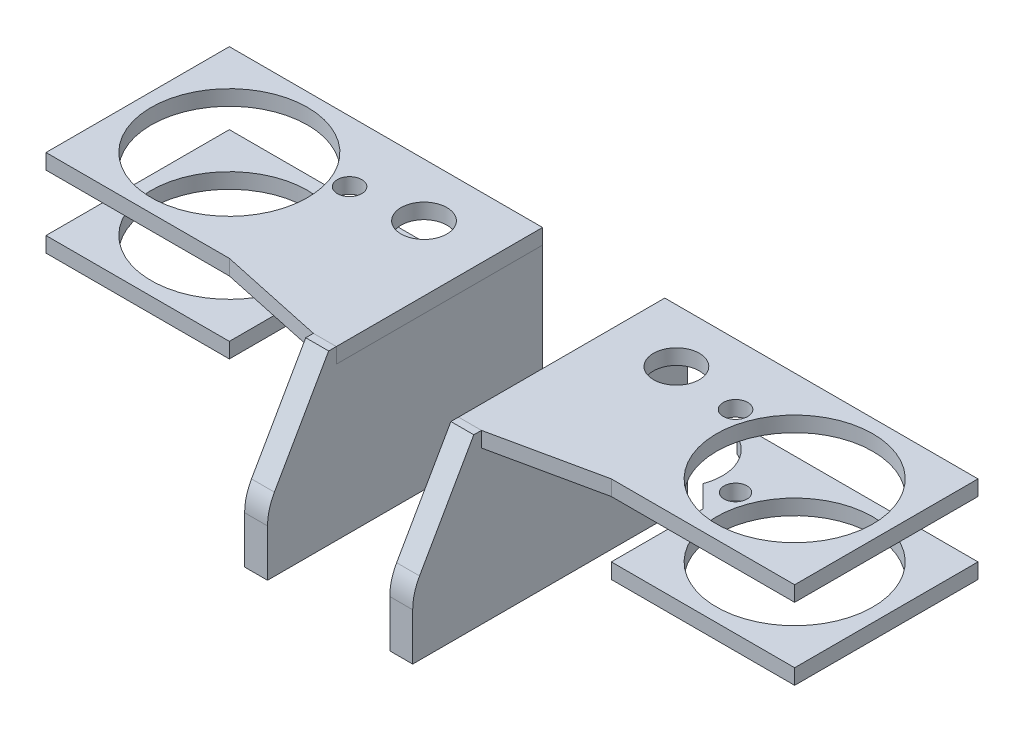
SolidWorks part; units mm, degrees
material "Alum Plate"
ref_plane "Front Plane" through (0, 0, 0) normal (0, 0, 1) x (1, 0, 0)
ref_plane "Top Plane" through (0, 0, 0) normal (0, 1, 0) x (1, 0, 0)
ref_plane "Right Plane" through (0, 0, 0) normal (1, 0, 0) x (0, 0, -1)
sketch "Sketch1" plane through (0, 0, 0) normal (0, 1, 0) x (1, 0, 0)
  line L0 (0, 0) -> (117.475, 0) construction
  line L1 (-117.475, 0) -> (0, 0) construction
  line L3 (-9.525, 158.75) -> (-3.175, 158.75)
  line L4 (-9.525, 158.75) -> (-9.525, 44.45)
  line L5 (-9.525, 44.45) -> (-3.175, 44.45)
  line L6 (-3.175, 158.75) -> (-3.175, 44.45)
  line L7 (-9.525, 158.75) -> (-3.175, 44.45) construction
  line L8 (-9.525, 44.45) -> (-3.175, 158.75) construction
  line L14 (-155.575, -76.2) -> (155.575, -76.2)
  line L18 (-117.475, 0) -> (-52.4506, 15.875) construction
  line L19 (52.4506, 15.875) -> (117.475, 0) construction
  line L20 (-25.4, 38.1) -> (0, 38.1) construction
  line L21 (-6.35, 101.6) -> (0, 101.6)
  line L29 (0, 0) -> (0, -25.4) construction
  line L30 (-117.475, 0) -> (-80.2096, 12.7) construction
  line L43 (-80.2096, 12.7) -> (-52.4506, 15.875) construction
  line L44 (52.4506, 15.875) -> (80.2096, 12.7) construction
  line L55 (80.2096, 12.7) -> (117.475, 0) construction
  line L69 (-155.575, -76.2) -> (-155.575, 38.1)
  line L70 (-155.575, 38.1) -> (155.575, 38.1)
  line L71 (155.575, -76.2) -> (155.575, 38.1)
  line L78 (0, 101.6) -> (0, -25.4)
  line L79 (0, -25.4) -> (0, -152.4) construction
  line L80 (-9.525, -209.55) -> (-3.175, -209.55) construction
  line L81 (-9.525, -209.55) -> (-9.525, -95.25) construction
  line L82 (-9.525, -95.25) -> (-3.175, -95.25) construction
  line L83 (-3.175, -209.55) -> (-3.175, -95.25) construction
  line L84 (-9.525, -209.55) -> (-3.175, -95.25) construction
  line L85 (-9.525, -95.25) -> (-3.175, -209.55) construction
  line L86 (0, -152.4) -> (-6.35, -152.4) construction
  line L87 (-34.925, -76.2) -> (-25.4, -76.2)
  line L88 (-34.925, -76.2) -> (-34.925, 38.1)
  line L89 (-34.925, 38.1) -> (-25.4, 38.1)
  line L90 (-25.4, -76.2) -> (-25.4, 38.1)
  line L91 (34.925, -76.2) -> (25.4, -76.2)
  line L92 (34.925, -76.2) -> (34.925, 38.1)
  line L93 (34.925, 38.1) -> (25.4, 38.1)
  line L94 (25.4, -76.2) -> (25.4, 38.1)
  line L95 (0, 38.1) -> (25.4, 38.1) construction
  circle A0 centre (-117.475, 0) radius 32.5
  circle A1 centre (-117.475, 0) radius 25
  circle A2 centre (117.475, 0) radius 32.5
  circle A3 centre (117.475, 0) radius 25
  circle A4 centre (-52.4506, 15.875) radius 17.5006
  circle A5 centre (52.4506, 15.875) radius 17.5006
  circle A6 centre (-80.2096, 12.7) radius 22.86
  circle A7 centre (80.2096, 12.7) radius 22.86
  point P8 (-6.35, 101.6)
  point P21 (117.475, 32.5)
  point P25 (52.4506, 33.3756)
  point P29 (52.4506, -1.6256)
  point P31 (0, -76.2)
  point P32 (-6.35, -152.4)
  point P62 (149.975, 0)
  dimension "D1" = 50
  dimension "D2" = 65
  dimension "D8" = 35.0012
  dimension "D11" = 127
  dimension "D12" = 63.5
  dimension "D17" = 45.72
  dimension "D3" = 114.3
  dimension "D4" = 6.35
  dimension "D5" = 234.95
  dimension "D6" = 38.1
  dimension "D7" = 38.1
  dimension "D9" = 114.3
  dimension "D10" = 9.525
  dimension "D13" = 9.525
  dimension "D14" = 50.8
  dimension "D15" = 27.94
  dimension "D16" = 39.37
  dimension "D18" = 22.225
  dimension "D19" = 25.4
sketch "Sketch2" plane through (0, 0, 0) normal (1, 0, 0) x (0, 0, -1)
  line L0 (0, 22.225) -> (0, 49.825) construction
  line L1 (-32.5, 53.325) -> (32.5, 53.325)
  line L2 (-32.5, 53.325) -> (-32.5, 46.325)
  line L3 (-32.5, 46.325) -> (32.5, 46.325)
  line L4 (32.5, 53.325) -> (32.5, 46.325)
  line L5 (-32.5, 53.325) -> (32.5, 46.325) construction
  line L6 (-32.5, 46.325) -> (32.5, 53.325) construction
  line L7 (-32.5, 82.55) -> (32.5, 82.55)
  line L8 (-32.5, 82.55) -> (-32.5, 75.55)
  line L9 (-32.5, 75.55) -> (32.5, 75.55)
  line L10 (32.5, 82.55) -> (32.5, 75.55)
  line L11 (-32.5, 82.55) -> (32.5, 75.55) construction
  line L12 (-32.5, 75.55) -> (32.5, 82.55) construction
  line L13 (-25.8191, 0) -> (33.9817, 0) construction
  line L14 (-25.4, 63.5) -> (-152.4, 63.5)
  line L15 (-76.2, 82.55) -> (38.1, 82.55)
  line L16 (-76.2, 82.55) -> (-76.2, 46.325)
  line L17 (-76.2, 46.325) -> (38.1, 46.325)
  line L18 (38.1, 82.55) -> (38.1, 46.325)
  line L19 (-16.2917, 28.7479) -> (-50.301, 31.6992) construction
  line L20 (17.0081, 33.1171) -> (-25.4, 63.5) construction
  line L21 (101.6, 0) -> (-25.4, 0) construction
  line L22 (-76.2, 76.2) -> (38.1, 76.2)
  line L23 (-76.2, 52.675) -> (38.1, 52.675)
  line L24 (-50.301, 31.6992) -> (-25.4, 63.5) construction
  line L25 (-129.1449, 47.625) -> (96, 47.625) construction
  line L32 (-76.2, 12.7) -> (38.1, 12.7)
  line L33 (-76.2, 12.7) -> (-76.2, 9.525)
  line L38 (-76.2, 9.525) -> (38.1, 9.525)
  line L39 (38.1, 12.7) -> (38.1, 9.525)
  line L40 (-1.6256, 31.6992) -> (33.3756, 31.6992)
  line L41 (-1.6256, 31.6992) -> (-1.6256, 76.2)
  line L42 (-1.6256, 76.2) -> (33.3756, 76.2)
  line L43 (33.3756, 31.6992) -> (33.3756, 76.2)
  line L44 (-1.6256, 31.6992) -> (33.3756, 76.2) construction
  line L45 (-1.6256, 76.2) -> (33.3756, 31.6992) construction
  line L46 (-38.1, 82.55) -> (-38.1, 46.325)
  line L47 (-38.1, 64.4375) -> (0, 64.4375) construction
  line L48 (0, 64.4375) -> (38.1, 64.4375) construction
  line L49 (-76.2, 12.7) -> (38.1, 9.525) construction
  line L50 (-76.2, 9.525) -> (38.1, 12.7) construction
  circle A0 centre (0, 22.225) radius 22.225
  circle A2 centre (-16.2917, 28.7479) radius 14
  circle A3 centre (-152.4, 63.5) radius 57.15
  circle A4 centre (-25.4, 63.5) radius 4.7625
  circle A5 centre (17.0081, 33.1171) radius 17.78
  circle A6 centre (-50.301, 31.6992) radius 18
  point P2 (0, 49.825)
  point P8 (0, 79.05)
  point P16 (34.7881, 33.1171)
  point P28 (-0.7719, 33.1171)
  point P32 (15.875, 53.9496)
  point P34 (-209.55, 63.5)
  point P35 (-30.2917, 28.7479)
  point P36 (-2.2917, 28.7479)
  point P55 (-32.301, 31.6992)
  point P57 (-19.05, 11.1125)
  point P67 (-68.301, 31.6992)
  dimension "D1" = 44.45
  dimension "D8" = 36
  dimension "D2" = 28
  dimension "D11" = 9.525
  dimension "D12" = 35.56
  dimension "D3" = 7
  dimension "D4" = 82.55
  dimension "D5" = 22.225
  dimension "D6" = 6.35
  dimension "D7" = 6.35
  dimension "D9" = 63.5
  dimension "D10" = 44.5008
  dimension "D13" = 15.875
  dimension "D15" = 3.175
  dimension "D16" = 50.8
sketch "Sketch5" plane through (0, 0, 0) normal (0, 1, 0) x (1, 0, 0)
  line L1 (-25.4, -2.2917) -> (21.59, -2.2917)
  line L2 (-25.4, -2.2917) -> (-25.4, -30.2917)
  line L3 (-25.4, -30.2917) -> (21.59, -30.2917)
  line L4 (21.59, -2.2917) -> (21.59, -30.2917)
  line L5 (-25.4, -2.2917) -> (21.59, -30.2917) construction
  line L6 (-25.4, -30.2917) -> (21.59, -2.2917) construction
  line L7 (8.255, 34.7881) -> (-31.75, 34.7881)
  line L8 (8.255, 34.7881) -> (8.255, -0.7719)
  line L9 (8.255, -0.7719) -> (-31.75, -0.7719)
  line L10 (-31.75, 34.7881) -> (-31.75, -0.7719)
  line L11 (8.255, 34.7881) -> (-31.75, -0.7719) construction
  line L12 (8.255, -0.7719) -> (-31.75, 34.7881) construction
  line L13 (-25.4, -32.301) -> (6.096, -32.301)
  line L14 (-25.4, -32.301) -> (-25.4, -68.301)
  line L15 (-25.4, -68.301) -> (6.096, -68.301)
  line L16 (6.096, -32.301) -> (6.096, -68.301)
  line L17 (-25.4, -32.301) -> (6.096, -68.301) construction
  line L18 (-25.4, -68.301) -> (6.096, -32.301) construction
  line L21 (-34.925, -76.2) -> (-34.925, 38.1) construction
  line L22 (-25.4, -76.2) -> (-25.4, 38.1) construction
  point P0 (-1.905, -16.2917)
  point P5 (-11.7475, 17.0081)
  point P10 (-9.652, -50.301)
  point P15 (-13.527, -3.175)
  point P16 (-22.0384, -16.2917)
  point P17 (-4.8852, -2.2917)
  point P19 (11.373, 0)
  point P21 (9.9064, -35.1019)
  point P22 (20.1032, -2.2917)
  point P23 (14.9373, -2.2917)
  point P27 (12.9506, -68.301)
  point P33 (-6.3174, -30.2917)
  point P34 (21.6277, -2.2917)
  point P35 (-20.7351, -2.2917)
  dimension "D1" = 40.005
  dimension "D2" = 46.99
  dimension "D3" = 3.175
  dimension "D6" = 31.496
ref_plane "Plane1" through (0, 76.2, 0) normal (0, 1, 0) x (1, 0, 0)
ref_plane "Plane2" through (0, 52.675, 0) normal (0, -1, 0) x (-1, 0, 0)
ref_plane "Plane3" through (25.4, 0, 0) normal (1, 0, 0) x (0, 0, -1)
sketch "Sketch6" plane through (25.4, 0, 0) normal (1, 0, 0) x (0, 0, -1)
  line L2 (-73.3496, 43.0143) -> (-50.8, 82.55)
  line L3 (-76.2, 82.55) -> (38.1, 82.55) construction
  line L4 (-50.8, 82.55) -> (-47.625, 82.55)
  line L5 (-47.625, 82.55) -> (-47.625, 76.2)
  line L6 (-76.2, 76.2) -> (38.1, 76.2) construction
  line L7 (-47.625, 76.2) -> (38.1, 76.2)
  line L8 (38.1, 76.2) -> (38.1, 12.7)
  line L10 (-76.2, 12.7) -> (38.1, 12.7) construction
  line L11 (-76.2, 12.7) -> (-76.2, 32.2634)
  line L12 (-76.2, 12.7) -> (38.1, 12.7)
  arc A3 (-76.2, 32.2634) -> (-73.3496, 43.0143) centre (-54.5002, 32.2634) cw
  point P6 (42.5063, 75.55)
  point P7 (-73.3496, 43.0143)
  dimension "D2" = 22.225
  dimension "D3" = 3.175
extrude "Boss-Extrude1" add sketch "Sketch6" along normal up to vertex (9.525 mm away) up to point (34.925, 0, -38.1)
sketch "Sketch7" plane through (0, 76.2, 0) normal (0, 1, 0) x (1, 0, 0)
  line L0 (25.4, -47.625) -> (34.925, -47.625)
  line L2 (155.575, -76.2) -> (155.575, 38.1) construction
  line L3 (155.575, -38.1) -> (155.575, 38.1)
  line L4 (155.575, 38.1) -> (25.4, 38.1)
  line L5 (25.4, 38.1) -> (25.4, -47.625)
  line L6 (155.575, -38.1) -> (79.375, -38.1)
  line L7 (79.375, -38.1) -> (34.925, -47.625)
  line L8 (117.475, 38.1) -> (117.475, 0) construction
  line L9 (117.475, 0) -> (117.475, -38.1) construction
  circle A0 centre (117.475, 0) radius 32.5 construction
  circle A1 centre (117.475, 0) radius 32.5
  circle A2 centre (80.2096, 12.7) radius 5.08
  circle A3 centre (52.4506, 15.875) radius 9.525
  dimension "D1" = 10.16
  dimension "D2" = 19.05
extrude "Boss-Extrude2" add sketch "Sketch7" along normal up to surface (6.35 mm away) separate body up to face at (30.1625, 82.55, 49.2125)
sketch "Sketch8" plane through (0, 52.675, 0) normal (0, -1, 0) x (-1, 0, 0)
  line L0 (-60.325, 33.2214) -> (-60.325, 38.1)
  line L1 (-79.375, -38.1) -> (-155.575, -38.1)
  line L2 (-79.375, -38.1) -> (-79.375, 38.1) construction
  line L3 (-79.375, 38.1) -> (-155.575, 38.1)
  line L4 (-155.575, -38.1) -> (-155.575, 38.1)
  line L5 (-79.375, -38.1) -> (-155.575, 38.1) construction
  line L6 (-79.375, 38.1) -> (-155.575, -38.1) construction
  line L7 (155.575, 38.1) -> (-155.575, 38.1) construction
  line L8 (-60.325, 38.1) -> (-79.375, 38.1)
  line L9 (-79.375, -38.1) -> (-79.375, 0)
  line L10 (-79.375, 0) -> (-70.2606, 9.1144)
  line L11 (-34.925, -76.2) -> (-34.925, 38.1) construction
  circle A0 centre (-117.475, 0) radius 32.5 construction
  circle A1 centre (-117.475, 0) radius 32.5
  arc A2 (-70.2606, 9.1144) -> (-60.325, 33.2214) centre (-52.4506, 15.875) cw
  circle A3 centre (-80.2096, 12.7) radius 4.7625
  dimension "D1" = 9.525
  dimension "D2" = 19.05
  dimension "D3" = 25.4
  dimension "D4" = 45
  dimension "D5" = 38.1
extrude "Boss-Extrude3" add sketch "Sketch8" along normal up to vertex (6.35 mm away) separate body up to point (0, 46.325, -38.1)
mirror "Mirror2" about plane through (0, 0, 0) normal (1, 0, 0) of bodies 106 108 111
